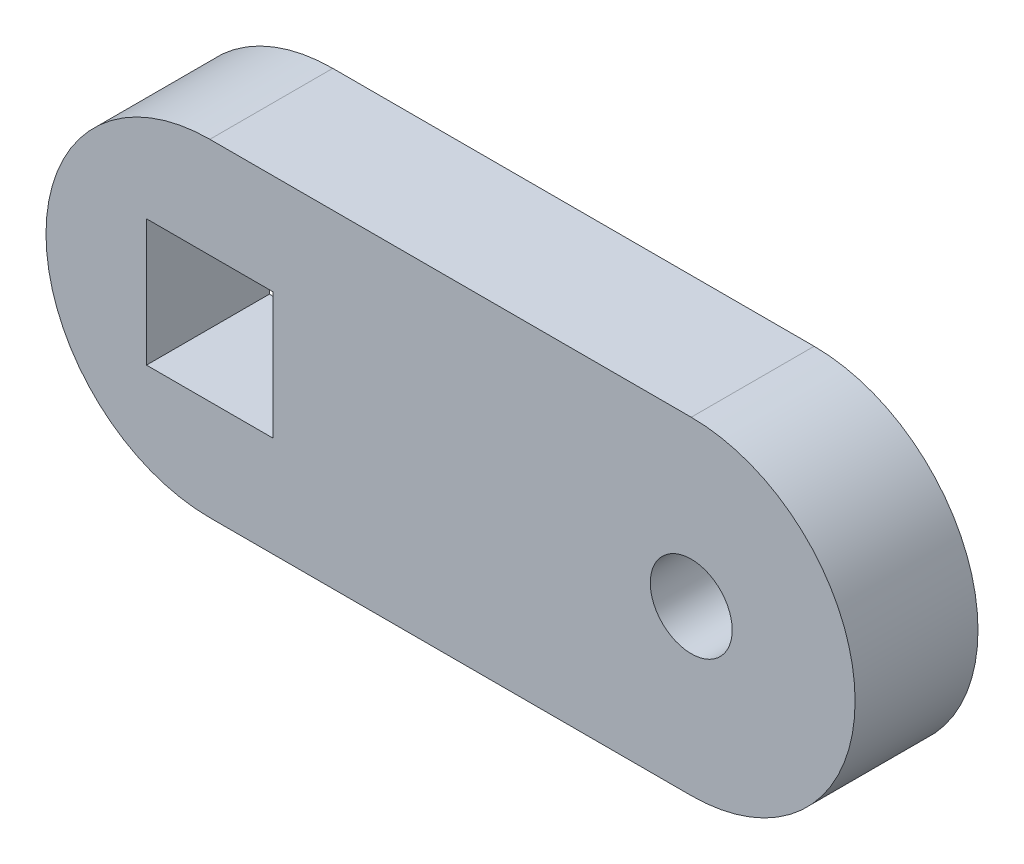
SolidWorks part; units mm, degrees
ref_plane "Front Plane" through (0, 0, 0) normal (0, 0, 1) x (1, 0, 0)
ref_plane "Top Plane" through (0, 0, 0) normal (0, 1, 0) x (1, 0, 0)
ref_plane "Right Plane" through (0, 0, 0) normal (1, 0, 0) x (0, 0, -1)
sketch "Model" plane through (0, 0, 0) normal (0, 0, 1) x (1, 0, 0)
  line L0 (29.6199, 13.7686) -> (29.6199, 16.8623)
  line L1 (29.6199, 16.8623) -> (23.4324, 16.8623)
  line L2 (23.4324, 16.8623) -> (23.4324, 10.6748)
  line L3 (23.4324, 10.6748) -> (29.6199, 10.6748)
  line L4 (29.6199, 10.6748) -> (29.6199, 13.7686)
  line L5 (26.5262, 21.7686) -> (50.0262, 21.7686)
  line L6 (26.5262, 5.7686) -> (50.0262, 5.7686)
  arc A0 (26.5262, 21.7686) -> (26.5262, 5.7686) centre (26.5262, 13.7686) ccw
  arc A1 (50.0262, 5.7686) -> (50.0262, 21.7686) centre (50.0262, 13.7686) ccw
  circle A2 centre (50.0262, 13.7686) radius 2
extrude "Boss-Extrude1" add sketch "Model" along normal blind 6 contours A0 L6 A1 L5 | L4 L0 L1 L2 L3 | A2
